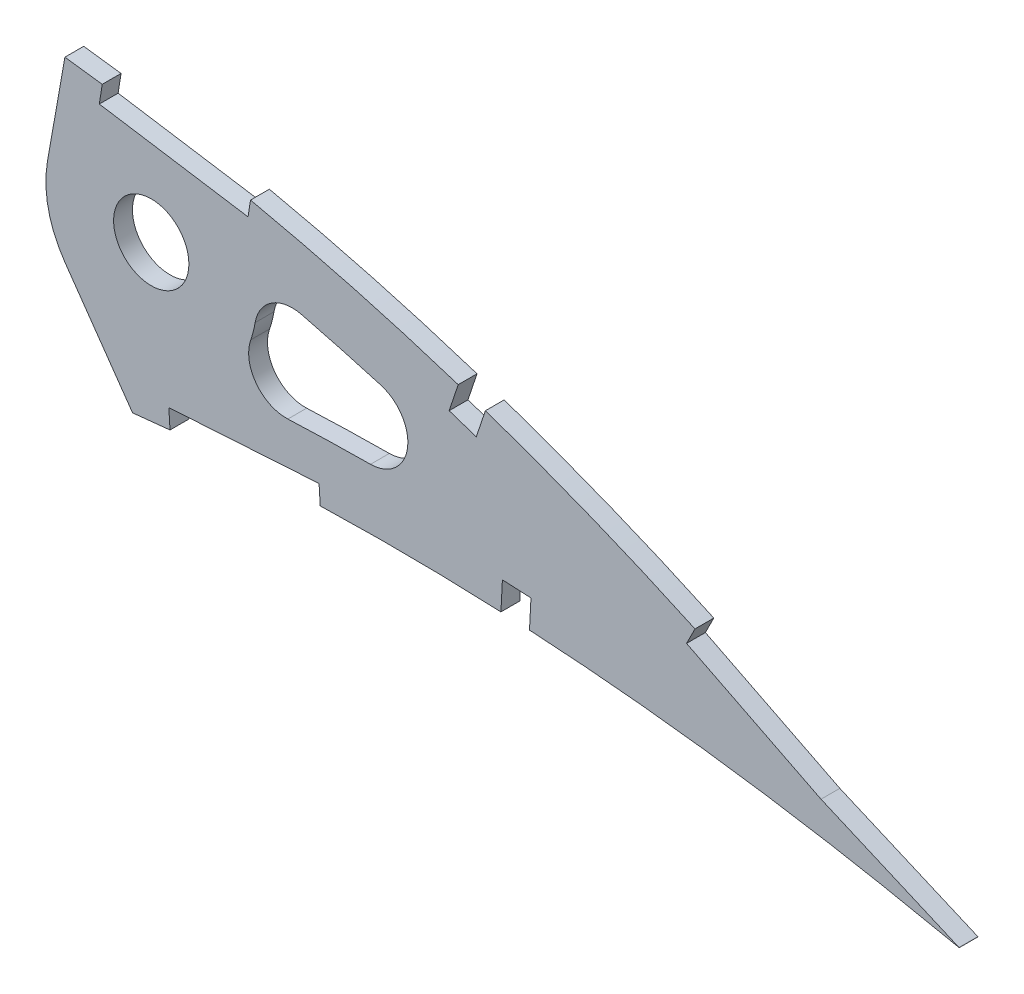
SolidWorks part; units mm, degrees
material "Pine"
ref_plane "Front Plane" through (0, 0, 0) normal (0, 0, 1) x (1, 0, 0)
ref_plane "Top Plane" through (0, 0, 0) normal (0, 1, 0) x (1, 0, 0)
ref_plane "Right Plane" through (0, 0, 0) normal (1, 0, 0) x (0, 0, -1)
curve "Curve1"
  spline degree 3 poles (0, 0, 0) (0.1249, -0.5894, 0) (0.3751, -1.7709, 0) (1.0551, -3.4717, 0) (1.9543, -5.1067, 0) (3.0917, -6.6716, 0) (4.4597, -8.1658, 0) (6.0551, -9.5909, 0) (7.8766, -10.9463, 0) (9.9217, -12.2312, 0) (12.1874, -13.447, 0) (14.6712, -14.593, 0) (17.3708, -15.6688, 0) (20.2833, -16.6729, 0) (23.4051, -17.607, 0) (26.7332, -18.4687, 0) (30.2639, -19.2592, 0) (33.9938, -19.9766, 0) (37.9188, -20.6214, 0) (42.0348, -21.1935, 0) (46.3376, -21.6931, 0) (50.823, -22.1192, 0) (55.4866, -22.4726, 0) (60.3236, -22.7538, 0) (65.3294, -22.9634, 0) (70.4993, -23.1008, 0) (75.828, -23.1681, 0) (81.3109, -23.1662, 0) (86.9426, -23.0948, 0) (92.7182, -22.9577, 0) (98.6323, -22.754, 0) (104.6794, -22.4863, 0) (110.8541, -22.1572, 0) (117.1509, -21.7679, 0) (123.5642, -21.32, 0) (130.0885, -20.8172, 0) (136.7178, -20.2607, 0) (143.4464, -19.6538, 0) (150.2683, -18.9994, 0) (157.1776, -18.2998, 0) (164.1682, -17.5581, 0) (171.2339, -16.7767, 0) (178.3687, -15.9599, 0) (185.566, -15.1091, 0) (192.8198, -14.2292, 0) (200.1233, -13.3218, 0) (207.4703, -12.3905, 0) (214.8542, -11.4396, 0) (222.2681, -10.469, 0) (229.7058, -9.4856, 0) (237.1601, -8.4887, 0) (244.6246, -7.4833, 0) (252.0922, -6.4726, 0) (259.5558, -5.4569, 0) (267.0088, -4.4404, 0) (274.4442, -3.4259, 0) (281.8548, -2.4135, 0) (289.2339, -1.4081, 0) (296.574, -0.4098, 0) (303.8684, 0.5795, 0) (311.1101, 1.5569, 0) (318.2922, 2.521, 0) (325.4074, 3.4714, 0) (332.4485, 4.4082, 0) (339.3029, 5.3032, 0) (345.9529, 6.204, 0) (352.4207, 6.9424, 0) (358.808, 7.5727, 0) (365.1214, 8.0894, 0) (371.3533, 8.5001, 0) (377.4966, 8.8075, 0) (383.544, 9.0161, 0) (389.4878, 9.132, 0) (395.3205, 9.1582, 0) (401.0343, 9.1029, 0) (406.6218, 8.9708, 0) (412.075, 8.7675, 0) (417.3864, 8.5002, 0) (422.5485, 8.1759, 0) (427.5535, 7.7996, 0) (432.3944, 7.38, 0) (437.0637, 6.9232, 0) (441.5544, 6.4344, 0) (445.8598, 5.924, 0) (449.973, 5.3952, 0) (453.8879, 4.8568, 0) (457.5982, 4.3142, 0) (461.0979, 3.7743, 0) (464.3817, 3.2423, 0) (467.4441, 2.7253, 0) (470.2803, 2.228, 0) (472.8856, 1.7553, 0) (475.2562, 1.3133, 0) (477.3874, 0.904, 0) (479.2765, 0.5343, 0) (480.9199, 0.2058, 0) (482.3151, -0.077, 0) (483.4599, -0.3128, 0) (484.3523, -0.4979, 0) (484.9907, -0.6325, 0) (485.3743, -0.7125, 0) (485.5448, -0.7489, 0) (485.5874, -0.758, 0) knots 0 0 0 0 0.003638 0.007293 0.011028 0.014901 0.018963 0.023258 0.027821 0.032679 0.037853 0.043362 0.049215 0.055422 0.061989 0.068918 0.076211 0.083868 0.091887 0.100266 0.109 0.118085 0.127515 0.137285 0.147388 0.157816 0.168563 0.179619 0.190977 0.202627 0.21456 0.226767 0.239236 0.251959 0.264924 0.27812 0.291536 0.30516 0.318981 0.332985 0.347163 0.361499 0.375981 0.390597 0.405333 0.420175 0.43511 0.450124 0.465203 0.480333 0.495501 0.51069 0.525887 0.541078 0.556247 0.571382 0.586466 0.601485 0.616424 0.631269 0.646007 0.660621 0.675098 0.689423 0.703582 0.716908 0.730009 0.742952 0.755726 0.76832 0.780724 0.792927 0.804916 0.816679 0.828204 0.839475 0.850481 0.861208 0.871639 0.881763 0.891564 0.901027 0.910139 0.918884 0.927249 0.935221 0.942785 0.949928 0.956638 0.962904 0.968712 0.974054 0.978918 0.983297 0.98718 0.990561 0.993433 0.995791 0.99763 0.998946 0.999737 1 1 1 1
curve "Curve2"
  spline degree 3 poles (486.1938, 0.758, 0) (486.1565, 0.781, 0) (486.0077, 0.8729, 0) (485.6723, 1.0786, 0) (485.1139, 1.4213, 0) (484.3321, 1.8984, 0) (483.3276, 2.5088, 0) (482.0999, 3.2482, 0) (480.6498, 4.1141, 0) (478.9775, 5.1026, 0) (477.0833, 6.2089, 0) (474.9678, 7.4286, 0) (472.6313, 8.7548, 0) (470.0748, 10.182, 0) (467.2989, 11.7035, 0) (464.3043, 13.3123, 0) (461.0921, 15.0004, 0) (457.6635, 16.7605, 0) (454.019, 18.5827, 0) (450.1605, 20.4596, 0) (446.0892, 22.3819, 0) (441.8065, 24.3391, 0) (437.3149, 26.3234, 0) (432.6155, 28.3224, 0) (427.7112, 30.3274, 0) (422.6039, 32.3272, 0) (417.2967, 34.3124, 0) (411.7916, 36.2703, 0) (406.0928, 38.1924, 0) (400.203, 40.0661, 0) (394.1264, 41.8812, 0) (387.8666, 43.626, 0) (381.4288, 45.2916, 0) (374.8171, 46.8658, 0) (368.037, 48.3381, 0) (361.0939, 49.6996, 0) (353.9938, 50.9366, 0) (346.7562, 52.0484, 0) (339.4976, 52.9732, 0) (332.2539, 53.8802, 0) (325.021, 54.7322, 0) (317.6998, 55.5482, 0) (310.2971, 56.3235, 0) (302.8205, 57.0556, 0) (295.2774, 57.7415, 0) (287.6757, 58.3791, 0) (280.0227, 58.9648, 0) (272.3266, 59.4977, 0) (264.5949, 59.9731, 0) (256.8359, 60.3907, 0) (249.0573, 60.7475, 0) (241.2675, 61.0411, 0) (233.4745, 61.2698, 0) (225.6865, 61.4312, 0) (217.912, 61.5245, 0) (210.159, 61.547, 0) (202.4359, 61.4984, 0) (194.7508, 61.377, 0) (187.1122, 61.1811, 0) (179.5282, 60.9103, 0) (172.0069, 60.5649, 0) (164.5567, 60.1418, 0) (157.1855, 59.6438, 0) (149.9016, 59.0688, 0) (142.713, 58.4167, 0) (135.6273, 57.6901, 0) (128.6522, 56.887, 0) (121.7954, 56.0099, 0) (115.0642, 55.0603, 0) (108.4663, 54.0378, 0) (102.0087, 52.9453, 0) (95.6983, 51.784, 0) (89.542, 50.5572, 0) (83.5463, 49.2652, 0) (77.7176, 47.912, 0) (72.062, 46.4999, 0) (66.5855, 45.0315, 0) (61.2937, 43.5103, 0) (56.192, 41.9397, 0) (51.2862, 40.3215, 0) (46.5802, 38.6618, 0) (42.0796, 36.9619, 0) (37.788, 35.2268, 0) (33.7103, 33.4591, 0) (29.8497, 31.6641, 0) (26.2104, 29.8437, 0) (22.7951, 28.0033, 0) (19.6072, 26.1454, 0) (16.6497, 24.2737, 0) (13.924, 22.3929, 0) (11.4337, 20.504, 0) (9.1798, 18.612, 0) (7.1636, 16.7197, 0) (5.388, 14.8284, 0) (3.8531, 12.9414, 0) (2.5606, 11.0602, 0) (1.511, 9.1866, 0) (0.7066, 7.3219, 0) (0.1466, 5.4673, 0) (-0.16, 3.6254, 0) (-0.2363, 1.7948, 0) (-0.0786, 0.5974, 0) (0, 0, 0) knots 0 0 0 0 0.000254 0.001015 0.002283 0.004057 0.006331 0.009105 0.012374 0.016134 0.02038 0.025106 0.030306 0.035972 0.0421 0.048678 0.055702 0.06316 0.071046 0.07935 0.088063 0.097176 0.106678 0.116562 0.126814 0.137428 0.148394 0.1597 0.171338 0.183298 0.19557 0.208144 0.221012 0.234162 0.247587 0.261277 0.275223 0.289414 0.303771 0.317689 0.331784 0.34604 0.360444 0.374983 0.38964 0.404403 0.419257 0.434187 0.449177 0.464215 0.479284 0.49437 0.509458 0.524532 0.539579 0.554583 0.56953 0.584403 0.599191 0.613877 0.628447 0.642889 0.657186 0.671326 0.685294 0.699078 0.712665 0.726043 0.739198 0.752118 0.764792 0.777208 0.789356 0.801224 0.812804 0.824083 0.835055 0.84571 0.856038 0.866034 0.875689 0.884998 0.893953 0.902553 0.910789 0.918661 0.926166 0.933303 0.940071 0.946475 0.952518 0.958205 0.963547 0.968557 0.97325 0.977651 0.981787 0.985694 0.989415 0.993001 0.996508 1 1 1 1
sketch "Sketch1" plane through (0, 0, 0) normal (0, 0, 1) x (1, 0, 0)
  line L10 (485.5874, -0.758) -> (490.1477, -1.6846)
  line L24 (486.1938, 0.758) -> (490.1477, -1.6846)
  spline S2 degree 3 poles (-3866.8103, -1018.8258) (79.7559, 75.3438) (-9.1933, 22.1629) (1.0551, -3.4717) (1.9543, -5.1067) (3.0917, -6.6716) (4.4597, -8.1658) (6.0551, -9.5909) (7.8766, -10.9463) (9.9217, -12.2312) (12.1874, -13.447) (14.6712, -14.593) (17.3708, -15.6688) (20.2833, -16.6729) (23.4051, -17.607) (26.7332, -18.4687) (30.2639, -19.2592) (33.9938, -19.9766) (37.9188, -20.6214) (42.0348, -21.1935) (46.3376, -21.6931) (50.823, -22.1192) (55.4866, -22.4726) (60.3236, -22.7538) (65.3294, -22.9634) (70.4993, -23.1008) (75.828, -23.1681) (81.3109, -23.1662) (86.9426, -23.0948) (92.7182, -22.9577) (98.6323, -22.754) (104.6794, -22.4863) (110.8541, -22.1572) (117.1509, -21.7679) (123.5642, -21.32) (130.0885, -20.8172) (136.7178, -20.2607) (143.4464, -19.6538) (150.2683, -18.9994) (157.1776, -18.2998) (164.1682, -17.5581) (171.2339, -16.7767) (178.3687, -15.9599) (185.566, -15.1091) (192.8198, -14.2292) (200.1233, -13.3218) (207.4703, -12.3905) (214.8542, -11.4396) (222.2681, -10.469) (229.7058, -9.4856) (237.1601, -8.4887) (244.6246, -7.4833) (252.0922, -6.4726) (259.5558, -5.4569) (267.0088, -4.4404) (274.4442, -3.4259) (281.8548, -2.4135) (289.2339, -1.4081) (296.574, -0.4098) (303.8684, 0.5795) (311.1101, 1.5569) (318.2922, 2.521) (325.4074, 3.4714) (332.4485, 4.4082) (339.3029, 5.3032) (345.9529, 6.204) (352.4207, 6.9424) (358.808, 7.5727) (365.1214, 8.0894) (371.3533, 8.5001) (377.4966, 8.8075) (383.544, 9.0161) (389.4878, 9.132) (395.3205, 9.1582) (401.0343, 9.1029) (406.6218, 8.9708) (412.075, 8.7675) (417.3864, 8.5002) (422.5485, 8.1759) (427.5535, 7.7996) (432.3944, 7.38) (437.0637, 6.9232) (441.5544, 6.4344) (445.8598, 5.924) (449.973, 5.3952) (453.8879, 4.8568) (457.5982, 4.3142) (461.0979, 3.7743) (464.3817, 3.2423) (467.4441, 2.7253) (470.2803, 2.228) (472.8856, 1.7553) (475.2562, 1.3133) (477.3874, 0.904) (479.2765, 0.5343) (480.9199, 0.2058) (482.3151, -0.077) (483.4599, -0.3128) (484.3523, -0.4979) (484.9907, -0.6325) (504.0158, -4.6034) (520.901, -17.6411) (1368.8084, 3899.3631) knots -0.155184 -0.155184 -0.155184 -0.155184 0.003638 0.007293 0.011028 0.014901 0.018963 0.023258 0.027821 0.032679 0.037853 0.043362 0.049215 0.055422 0.061989 0.068918 0.076211 0.083868 0.091887 0.100266 0.109 0.118085 0.127515 0.137285 0.147388 0.157816 0.168563 0.179619 0.190977 0.202627 0.21456 0.226767 0.239236 0.251959 0.264924 0.27812 0.291536 0.30516 0.318981 0.332985 0.347163 0.361499 0.375981 0.390597 0.405333 0.420175 0.43511 0.450124 0.465203 0.480333 0.495501 0.51069 0.525887 0.541078 0.556247 0.571382 0.586466 0.601485 0.616424 0.631269 0.646007 0.660621 0.675098 0.689423 0.703582 0.716908 0.730009 0.742952 0.755726 0.76832 0.780724 0.792927 0.804916 0.816679 0.828204 0.839475 0.850481 0.861208 0.871639 0.881763 0.891564 0.901027 0.910139 0.918884 0.927249 0.935221 0.942785 0.949928 0.956638 0.962904 0.968712 0.974054 0.978918 0.983297 0.98718 0.990561 0.993433 0.995791 0.99763 0.998946 0.999737 1.115177 1.115177 1.115177 1.115177 only from (0, 0) to (485.5874, -0.758) construction
  spline S3 degree 3 poles (2637.6242, 3371.1949) (518.0891, -28.6046) (504.1645, -10.2642) (485.6723, 1.0786) (485.1139, 1.4213) (484.3321, 1.8984) (483.3276, 2.5088) (482.0999, 3.2482) (480.6498, 4.1141) (478.9775, 5.1026) (477.0833, 6.2089) (474.9678, 7.4286) (472.6313, 8.7548) (470.0748, 10.182) (467.2989, 11.7035) (464.3043, 13.3123) (461.0921, 15.0004) (457.6635, 16.7605) (454.019, 18.5827) (450.1605, 20.4596) (446.0892, 22.3819) (441.8065, 24.3391) (437.3149, 26.3234) (432.6155, 28.3224) (427.7112, 30.3274) (422.6039, 32.3272) (417.2967, 34.3124) (411.7916, 36.2703) (406.0928, 38.1924) (400.203, 40.0661) (394.1264, 41.8812) (387.8666, 43.626) (381.4288, 45.2916) (374.8171, 46.8658) (368.037, 48.3381) (361.0939, 49.6996) (353.9938, 50.9366) (346.7562, 52.0484) (339.4976, 52.9732) (332.2539, 53.8802) (325.021, 54.7322) (317.6998, 55.5482) (310.2971, 56.3235) (302.8205, 57.0556) (295.2774, 57.7415) (287.6757, 58.3791) (280.0227, 58.9648) (272.3266, 59.4977) (264.5949, 59.9731) (256.8359, 60.3907) (249.0573, 60.7475) (241.2675, 61.0411) (233.4745, 61.2698) (225.6865, 61.4312) (217.912, 61.5245) (210.159, 61.547) (202.4359, 61.4984) (194.7508, 61.377) (187.1122, 61.1811) (179.5282, 60.9103) (172.0069, 60.5649) (164.5567, 60.1418) (157.1855, 59.6438) (149.9016, 59.0688) (142.713, 58.4167) (135.6273, 57.6901) (128.6522, 56.887) (121.7954, 56.0099) (115.0642, 55.0603) (108.4663, 54.0378) (102.0087, 52.9453) (95.6983, 51.784) (89.542, 50.5572) (83.5463, 49.2652) (77.7176, 47.912) (72.062, 46.4999) (66.5855, 45.0315) (61.2937, 43.5103) (56.192, 41.9397) (51.2862, 40.3215) (46.5802, 38.6618) (42.0796, 36.9619) (37.788, 35.2268) (33.7103, 33.4591) (29.8497, 31.6641) (26.2104, 29.8437) (22.7951, 28.0033) (19.6072, 26.1454) (16.6497, 24.2737) (13.924, 22.3929) (11.4337, 20.504) (9.1798, 18.612) (7.1636, 16.7197) (5.388, 14.8284) (3.8531, 12.9414) (2.5606, 11.0602) (1.511, 9.1866) (0.7066, 7.3219) (0.1466, 5.4673) (-0.16, 3.6254) (-1.3078, -23.9112) (100.477, -44.4073) (-3985.5392, -325.5751) knots -0.123624 -0.123624 -0.123624 -0.123624 0.000254 0.001015 0.002283 0.004057 0.006331 0.009105 0.012374 0.016134 0.02038 0.025106 0.030306 0.035972 0.0421 0.048678 0.055702 0.06316 0.071046 0.07935 0.088063 0.097176 0.106678 0.116562 0.126814 0.137428 0.148394 0.1597 0.171338 0.183298 0.19557 0.208144 0.221012 0.234162 0.247587 0.261277 0.275223 0.289414 0.303771 0.317689 0.331784 0.34604 0.360444 0.374983 0.38964 0.404403 0.419257 0.434187 0.449177 0.464215 0.479284 0.49437 0.509458 0.524532 0.539579 0.554583 0.56953 0.584403 0.599191 0.613877 0.628447 0.642889 0.657186 0.671326 0.685294 0.699078 0.712665 0.726043 0.739198 0.752118 0.764792 0.777208 0.789356 0.801224 0.812804 0.824083 0.835055 0.84571 0.856038 0.866034 0.875689 0.884998 0.893953 0.902553 0.910789 0.918661 0.926166 0.933303 0.940071 0.946475 0.952518 0.958205 0.963547 0.968557 0.97325 0.977651 0.981787 0.985694 0.989415 0.993001 0.996508 1.148636 1.148636 1.148636 1.148636 only from (486.1938, 0.758) to (0, 0) construction
  spline S4 degree 3 poles (0, 0) (0.1249, -0.5894) (0.3751, -1.7709) (1.0551, -3.4717) (1.9543, -5.1067) (3.0917, -6.6716) (4.4597, -8.1658) (6.0551, -9.5909) (7.8766, -10.9463) (9.9217, -12.2312) (12.1874, -13.447) (14.6712, -14.593) (17.3708, -15.6688) (20.2833, -16.6729) (23.4051, -17.607) (26.7332, -18.4687) (30.2639, -19.2592) (33.9938, -19.9766) (37.9188, -20.6214) (42.0348, -21.1935) (46.3376, -21.6931) (50.823, -22.1192) (55.4866, -22.4726) (60.3236, -22.7538) (65.3294, -22.9634) (70.4993, -23.1008) (75.828, -23.1681) (81.3109, -23.1662) (86.9426, -23.0948) (92.7182, -22.9577) (98.6323, -22.754) (104.6794, -22.4863) (110.8541, -22.1572) (117.1509, -21.7679) (123.5642, -21.32) (130.0885, -20.8172) (136.7178, -20.2607) (143.4464, -19.6538) (150.2683, -18.9994) (157.1776, -18.2998) (164.1682, -17.5581) (171.2339, -16.7767) (178.3687, -15.9599) (185.566, -15.1091) (192.8198, -14.2292) (200.1233, -13.3218) (207.4703, -12.3905) (214.8542, -11.4396) (222.2681, -10.469) (229.7058, -9.4856) (237.1601, -8.4887) (244.6246, -7.4833) (252.0922, -6.4726) (259.5558, -5.4569) (267.0088, -4.4404) (274.4442, -3.4259) (281.8548, -2.4135) (289.2339, -1.4081) (296.574, -0.4098) (303.8684, 0.5795) (311.1101, 1.5569) (318.2922, 2.521) (325.4074, 3.4714) (332.4485, 4.4082) (339.3029, 5.3032) (345.9529, 6.204) (352.4207, 6.9424) (358.808, 7.5727) (365.1214, 8.0894) (371.3533, 8.5001) (377.4966, 8.8075) (383.544, 9.0161) (389.4878, 9.132) (395.3205, 9.1582) (401.0343, 9.1029) (406.6218, 8.9708) (412.075, 8.7675) (417.3864, 8.5002) (422.5485, 8.1759) (427.5535, 7.7996) (432.3944, 7.38) (437.0637, 6.9232) (441.5544, 6.4344) (445.8598, 5.924) (449.973, 5.3952) (453.8879, 4.8568) (457.5982, 4.3142) (461.0979, 3.7743) (464.3817, 3.2423) (467.4441, 2.7253) (470.2803, 2.228) (472.8856, 1.7553) (475.2562, 1.3133) (477.3874, 0.904) (479.2765, 0.5343) (480.9199, 0.2058) (482.3151, -0.077) (483.4599, -0.3128) (484.3523, -0.4979) (484.9907, -0.6325) (485.3743, -0.7125) (485.5448, -0.7489) (485.5874, -0.758) knots 0 0 0 0 0.003638 0.007293 0.011028 0.014901 0.018963 0.023258 0.027821 0.032679 0.037853 0.043362 0.049215 0.055422 0.061989 0.068918 0.076211 0.083868 0.091887 0.100266 0.109 0.118085 0.127515 0.137285 0.147388 0.157816 0.168563 0.179619 0.190977 0.202627 0.21456 0.226767 0.239236 0.251959 0.264924 0.27812 0.291536 0.30516 0.318981 0.332985 0.347163 0.361499 0.375981 0.390597 0.405333 0.420175 0.43511 0.450124 0.465203 0.480333 0.495501 0.51069 0.525887 0.541078 0.556247 0.571382 0.586466 0.601485 0.616424 0.631269 0.646007 0.660621 0.675098 0.689423 0.703582 0.716908 0.730009 0.742952 0.755726 0.76832 0.780724 0.792927 0.804916 0.816679 0.828204 0.839475 0.850481 0.861208 0.871639 0.881763 0.891564 0.901027 0.910139 0.918884 0.927249 0.935221 0.942785 0.949928 0.956638 0.962904 0.968712 0.974054 0.978918 0.983297 0.98718 0.990561 0.993433 0.995791 0.99763 0.998946 0.999737 1 1 1 1
  spline S5 degree 3 poles (486.1938, 0.758) (486.1565, 0.781) (486.0077, 0.8729) (485.6723, 1.0786) (485.1139, 1.4213) (484.3321, 1.8984) (483.3276, 2.5088) (482.0999, 3.2482) (480.6498, 4.1141) (478.9775, 5.1026) (477.0833, 6.2089) (474.9678, 7.4286) (472.6313, 8.7548) (470.0748, 10.182) (467.2989, 11.7035) (464.3043, 13.3123) (461.0921, 15.0004) (457.6635, 16.7605) (454.019, 18.5827) (450.1605, 20.4596) (446.0892, 22.3819) (441.8065, 24.3391) (437.3149, 26.3234) (432.6155, 28.3224) (427.7112, 30.3274) (422.6039, 32.3272) (417.2967, 34.3124) (411.7916, 36.2703) (406.0928, 38.1924) (400.203, 40.0661) (394.1264, 41.8812) (387.8666, 43.626) (381.4288, 45.2916) (374.8171, 46.8658) (368.037, 48.3381) (361.0939, 49.6996) (353.9938, 50.9366) (346.7562, 52.0484) (339.4976, 52.9732) (332.2539, 53.8802) (325.021, 54.7322) (317.6998, 55.5482) (310.2971, 56.3235) (302.8205, 57.0556) (295.2774, 57.7415) (287.6757, 58.3791) (280.0227, 58.9648) (272.3266, 59.4977) (264.5949, 59.9731) (256.8359, 60.3907) (249.0573, 60.7475) (241.2675, 61.0411) (233.4745, 61.2698) (225.6865, 61.4312) (217.912, 61.5245) (210.159, 61.547) (202.4359, 61.4984) (194.7508, 61.377) (187.1122, 61.1811) (179.5282, 60.9103) (172.0069, 60.5649) (164.5567, 60.1418) (157.1855, 59.6438) (149.9016, 59.0688) (142.713, 58.4167) (135.6273, 57.6901) (128.6522, 56.887) (121.7954, 56.0099) (115.0642, 55.0603) (108.4663, 54.0378) (102.0087, 52.9453) (95.6983, 51.784) (89.542, 50.5572) (83.5463, 49.2652) (77.7176, 47.912) (72.062, 46.4999) (66.5855, 45.0315) (61.2937, 43.5103) (56.192, 41.9397) (51.2862, 40.3215) (46.5802, 38.6618) (42.0796, 36.9619) (37.788, 35.2268) (33.7103, 33.4591) (29.8497, 31.6641) (26.2104, 29.8437) (22.7951, 28.0033) (19.6072, 26.1454) (16.6497, 24.2737) (13.924, 22.3929) (11.4337, 20.504) (9.1798, 18.612) (7.1636, 16.7197) (5.388, 14.8284) (3.8531, 12.9414) (2.5606, 11.0602) (1.511, 9.1866) (0.7066, 7.3219) (0.1466, 5.4673) (-0.16, 3.6254) (-0.2363, 1.7948) (-0.0786, 0.5974) (0, 0) knots 0 0 0 0 0.000254 0.001015 0.002283 0.004057 0.006331 0.009105 0.012374 0.016134 0.02038 0.025106 0.030306 0.035972 0.0421 0.048678 0.055702 0.06316 0.071046 0.07935 0.088063 0.097176 0.106678 0.116562 0.126814 0.137428 0.148394 0.1597 0.171338 0.183298 0.19557 0.208144 0.221012 0.234162 0.247587 0.261277 0.275223 0.289414 0.303771 0.317689 0.331784 0.34604 0.360444 0.374983 0.38964 0.404403 0.419257 0.434187 0.449177 0.464215 0.479284 0.49437 0.509458 0.524532 0.539579 0.554583 0.56953 0.584403 0.599191 0.613877 0.628447 0.642889 0.657186 0.671326 0.685294 0.699078 0.712665 0.726043 0.739198 0.752118 0.764792 0.777208 0.789356 0.801224 0.812804 0.824083 0.835055 0.84571 0.856038 0.866034 0.875689 0.884998 0.893953 0.902553 0.910789 0.918661 0.926166 0.933303 0.940071 0.946475 0.952518 0.958205 0.963547 0.968557 0.97325 0.977651 0.981787 0.985694 0.989415 0.993001 0.996508 1 1 1 1
extrude "Boss-Extrude1" add sketch "Sketch1" along normal blind 3.175
sketch "Sketch5" plane through (0, 0, 3.175) normal (0, 0, 1) x (1, 0, 0)
  line L0 (336.323, 36.32) -> (339.2642, 53)
  line L1 (339.2684, 23.0344) -> (350.6801, 6.7368)
  line L2 (353.8329, 33.2326) -> (374.466, 33.2326)
  circle A0 centre (353.8329, 33.2326) radius 6.35
  circle A1 centre (353.8329, 33.2326) radius 6.35
  circle A2 centre (353.8329, 33.2326) radius 17.78
  spline S0 degree 3 poles (-1939.0794, -487.5307) (48.5631, 55.4905) (-7.2206, 17.2286) (1.0551, -3.4717) (1.9543, -5.1067) (3.0917, -6.6716) (4.4597, -8.1658) (6.0551, -9.5909) (7.8766, -10.9463) (9.9217, -12.2312) (12.1874, -13.447) (14.6712, -14.593) (17.3708, -15.6688) (20.2833, -16.6729) (23.4051, -17.607) (26.7332, -18.4687) (30.2639, -19.2592) (33.9938, -19.9766) (37.9188, -20.6214) (42.0348, -21.1935) (46.3376, -21.6931) (50.823, -22.1192) (55.4866, -22.4726) (60.3236, -22.7538) (65.3294, -22.9634) (70.4993, -23.1008) (75.828, -23.1681) (81.3109, -23.1662) (86.9426, -23.0948) (92.7182, -22.9577) (98.6323, -22.754) (104.6794, -22.4863) (110.8541, -22.1572) (117.1509, -21.7679) (123.5642, -21.32) (130.0885, -20.8172) (136.7178, -20.2607) (143.4464, -19.6538) (150.2683, -18.9994) (157.1776, -18.2998) (164.1682, -17.5581) (171.2339, -16.7767) (178.3687, -15.9599) (185.566, -15.1091) (192.8198, -14.2292) (200.1233, -13.3218) (207.4703, -12.3905) (214.8542, -11.4396) (222.2681, -10.469) (229.7058, -9.4856) (237.1601, -8.4887) (244.6246, -7.4833) (252.0922, -6.4726) (259.5558, -5.4569) (267.0088, -4.4404) (274.4442, -3.4259) (281.8548, -2.4135) (289.2339, -1.4081) (296.574, -0.4098) (303.8684, 0.5795) (311.1101, 1.5569) (318.2922, 2.521) (325.4074, 3.4714) (332.4485, 4.4082) (339.3029, 5.3032) (345.9529, 6.204) (352.4207, 6.9424) (358.808, 7.5727) (365.1214, 8.0894) (371.3533, 8.5001) (377.4966, 8.8075) (383.544, 9.0161) (389.4878, 9.132) (395.3205, 9.1582) (401.0343, 9.1029) (406.6218, 8.9708) (412.075, 8.7675) (417.3864, 8.5002) (422.5485, 8.1759) (427.5535, 7.7996) (432.3944, 7.38) (437.0637, 6.9232) (441.5544, 6.4344) (445.8598, 5.924) (449.973, 5.3952) (453.8879, 4.8568) (457.5982, 4.3142) (461.0979, 3.7743) (464.3817, 3.2423) (467.4441, 2.7253) (470.2803, 2.228) (472.8856, 1.7553) (475.2562, 1.3133) (477.3874, 0.904) (479.2765, 0.5343) (480.9199, 0.2058) (482.3151, -0.077) (483.4599, -0.3128) (484.3523, -0.4979) (484.9907, -0.6325) (500.1693, -3.8005) (513.9154, -12.6904) (943.5402, 1945.4943) knots -0.123191 -0.123191 -0.123191 -0.123191 0.003638 0.007293 0.011028 0.014901 0.018963 0.023258 0.027821 0.032679 0.037853 0.043362 0.049215 0.055422 0.061989 0.068918 0.076211 0.083868 0.091887 0.100266 0.109 0.118085 0.127515 0.137285 0.147388 0.157816 0.168563 0.179619 0.190977 0.202627 0.21456 0.226767 0.239236 0.251959 0.264924 0.27812 0.291536 0.30516 0.318981 0.332985 0.347163 0.361499 0.375981 0.390597 0.405333 0.420175 0.43511 0.450124 0.465203 0.480333 0.495501 0.51069 0.525887 0.541078 0.556247 0.571382 0.586466 0.601485 0.616424 0.631269 0.646007 0.660621 0.675098 0.689423 0.703582 0.716908 0.730009 0.742952 0.755726 0.76832 0.780724 0.792927 0.804916 0.816679 0.828204 0.839475 0.850481 0.861208 0.871639 0.881763 0.891564 0.901027 0.910139 0.918884 0.927249 0.935221 0.942785 0.949928 0.956638 0.962904 0.968712 0.974054 0.978918 0.983297 0.98718 0.990561 0.993433 0.995791 0.99763 0.998946 0.999737 1.091411 1.091411 1.091411 1.091411 only from (0, 0) to (485.5874, -0.758) construction
  spline S1 degree 3 poles (1577.8242, 1676.0308) (512.2068, -21.3963) (500.4185, -7.9664) (485.6723, 1.0786) (485.1139, 1.4213) (484.3321, 1.8984) (483.3276, 2.5088) (482.0999, 3.2482) (480.6498, 4.1141) (478.9775, 5.1026) (477.0833, 6.2089) (474.9678, 7.4286) (472.6313, 8.7548) (470.0748, 10.182) (467.2989, 11.7035) (464.3043, 13.3123) (461.0921, 15.0004) (457.6635, 16.7605) (454.019, 18.5827) (450.1605, 20.4596) (446.0892, 22.3819) (441.8065, 24.3391) (437.3149, 26.3234) (432.6155, 28.3224) (427.7112, 30.3274) (422.6039, 32.3272) (417.2967, 34.3124) (411.7916, 36.2703) (406.0928, 38.1924) (400.203, 40.0661) (394.1264, 41.8812) (387.8666, 43.626) (381.4288, 45.2916) (374.8171, 46.8658) (368.037, 48.3381) (361.0939, 49.6996) (353.9938, 50.9366) (346.7562, 52.0484) (339.4976, 52.9732) (332.2539, 53.8802) (325.021, 54.7322) (317.6998, 55.5482) (310.2971, 56.3235) (302.8205, 57.0556) (295.2774, 57.7415) (287.6757, 58.3791) (280.0227, 58.9648) (272.3266, 59.4977) (264.5949, 59.9731) (256.8359, 60.3907) (249.0573, 60.7475) (241.2675, 61.0411) (233.4745, 61.2698) (225.6865, 61.4312) (217.912, 61.5245) (210.159, 61.547) (202.4359, 61.4984) (194.7508, 61.377) (187.1122, 61.1811) (179.5282, 60.9103) (172.0069, 60.5649) (164.5567, 60.1418) (157.1855, 59.6438) (149.9016, 59.0688) (142.713, 58.4167) (135.6273, 57.6901) (128.6522, 56.887) (121.7954, 56.0099) (115.0642, 55.0603) (108.4663, 54.0378) (102.0087, 52.9453) (95.6983, 51.784) (89.542, 50.5572) (83.5463, 49.2652) (77.7176, 47.912) (72.062, 46.4999) (66.5855, 45.0315) (61.2937, 43.5103) (56.192, 41.9397) (51.2862, 40.3215) (46.5802, 38.6618) (42.0796, 36.9619) (37.788, 35.2268) (33.7103, 33.4591) (29.8497, 31.6641) (26.2104, 29.8437) (22.7951, 28.0033) (19.6072, 26.1454) (16.6497, 24.2737) (13.924, 22.3929) (11.4337, 20.504) (9.1798, 18.612) (7.1636, 16.7197) (5.388, 14.8284) (3.8531, 12.9414) (2.5606, 11.0602) (1.511, 9.1866) (0.7066, 7.3219) (0.1466, 5.4673) (-0.16, 3.6254) (-1.0869, -18.6116) (64.385, -36.0874) (-1990.8444, -185.2686) knots -0.098119 -0.098119 -0.098119 -0.098119 0.000254 0.001015 0.002283 0.004057 0.006331 0.009105 0.012374 0.016134 0.02038 0.025106 0.030306 0.035972 0.0421 0.048678 0.055702 0.06316 0.071046 0.07935 0.088063 0.097176 0.106678 0.116562 0.126814 0.137428 0.148394 0.1597 0.171338 0.183298 0.19557 0.208144 0.221012 0.234162 0.247587 0.261277 0.275223 0.289414 0.303771 0.317689 0.331784 0.34604 0.360444 0.374983 0.38964 0.404403 0.419257 0.434187 0.449177 0.464215 0.479284 0.49437 0.509458 0.524532 0.539579 0.554583 0.56953 0.584403 0.599191 0.613877 0.628447 0.642889 0.657186 0.671326 0.685294 0.699078 0.712665 0.726043 0.739198 0.752118 0.764792 0.777208 0.789356 0.801224 0.812804 0.824083 0.835055 0.84571 0.856038 0.866034 0.875689 0.884998 0.893953 0.902553 0.910789 0.918661 0.926166 0.933303 0.940071 0.946475 0.952518 0.958205 0.963547 0.968557 0.97325 0.977651 0.981787 0.985694 0.989415 0.993001 0.996508 1.117993 1.117993 1.117993 1.117993 only from (486.1938, 0.758) to (0, 0) construction
  spline S2 degree 3 poles (0, 0) (0.1249, -0.5894) (0.3751, -1.7709) (1.0551, -3.4717) (1.9543, -5.1067) (3.0917, -6.6716) (4.4597, -8.1658) (6.0551, -9.5909) (7.8766, -10.9463) (9.9217, -12.2312) (12.1874, -13.447) (14.6712, -14.593) (17.3708, -15.6688) (20.2833, -16.6729) (23.4051, -17.607) (26.7332, -18.4687) (30.2639, -19.2592) (33.9938, -19.9766) (37.9188, -20.6214) (42.0348, -21.1935) (46.3376, -21.6931) (50.823, -22.1192) (55.4866, -22.4726) (60.3236, -22.7538) (65.3294, -22.9634) (70.4993, -23.1008) (75.828, -23.1681) (81.3109, -23.1662) (86.9426, -23.0948) (92.7182, -22.9577) (98.6323, -22.754) (104.6794, -22.4863) (110.8541, -22.1572) (117.1509, -21.7679) (123.5642, -21.32) (130.0885, -20.8172) (136.7178, -20.2607) (143.4464, -19.6538) (150.2683, -18.9994) (157.1776, -18.2998) (164.1682, -17.5581) (171.2339, -16.7767) (178.3687, -15.9599) (185.566, -15.1091) (192.8198, -14.2292) (200.1233, -13.3218) (207.4703, -12.3905) (214.8542, -11.4396) (222.2681, -10.469) (229.7058, -9.4856) (237.1601, -8.4887) (244.6246, -7.4833) (252.0922, -6.4726) (259.5558, -5.4569) (267.0088, -4.4404) (274.4442, -3.4259) (281.8548, -2.4135) (289.2339, -1.4081) (296.574, -0.4098) (303.8684, 0.5795) (311.1101, 1.5569) (318.2922, 2.521) (325.4074, 3.4714) (332.4485, 4.4082) (339.3029, 5.3032) (345.9529, 6.204) (352.4207, 6.9424) (358.808, 7.5727) (365.1214, 8.0894) (371.3533, 8.5001) (377.4966, 8.8075) (383.544, 9.0161) (389.4878, 9.132) (395.3205, 9.1582) (401.0343, 9.1029) (406.6218, 8.9708) (412.075, 8.7675) (417.3864, 8.5002) (422.5485, 8.1759) (427.5535, 7.7996) (432.3944, 7.38) (437.0637, 6.9232) (441.5544, 6.4344) (445.8598, 5.924) (449.973, 5.3952) (453.8879, 4.8568) (457.5982, 4.3142) (461.0979, 3.7743) (464.3817, 3.2423) (467.4441, 2.7253) (470.2803, 2.228) (472.8856, 1.7553) (475.2562, 1.3133) (477.3874, 0.904) (479.2765, 0.5343) (480.9199, 0.2058) (482.3151, -0.077) (483.4599, -0.3128) (484.3523, -0.4979) (484.9907, -0.6325) (485.3743, -0.7125) (485.5448, -0.7489) (485.5874, -0.758) knots 0 0 0 0 0.003638 0.007293 0.011028 0.014901 0.018963 0.023258 0.027821 0.032679 0.037853 0.043362 0.049215 0.055422 0.061989 0.068918 0.076211 0.083868 0.091887 0.100266 0.109 0.118085 0.127515 0.137285 0.147388 0.157816 0.168563 0.179619 0.190977 0.202627 0.21456 0.226767 0.239236 0.251959 0.264924 0.27812 0.291536 0.30516 0.318981 0.332985 0.347163 0.361499 0.375981 0.390597 0.405333 0.420175 0.43511 0.450124 0.465203 0.480333 0.495501 0.51069 0.525887 0.541078 0.556247 0.571382 0.586466 0.601485 0.616424 0.631269 0.646007 0.660621 0.675098 0.689423 0.703582 0.716908 0.730009 0.742952 0.755726 0.76832 0.780724 0.792927 0.804916 0.816679 0.828204 0.839475 0.850481 0.861208 0.871639 0.881763 0.891564 0.901027 0.910139 0.918884 0.927249 0.935221 0.942785 0.949928 0.956638 0.962904 0.968712 0.974054 0.978918 0.983297 0.98718 0.990561 0.993433 0.995791 0.99763 0.998946 0.999737 1 1 1 1
  spline S3 degree 3 poles (486.1938, 0.758) (486.1565, 0.781) (486.0077, 0.8729) (485.6723, 1.0786) (485.1139, 1.4213) (484.3321, 1.8984) (483.3276, 2.5088) (482.0999, 3.2482) (480.6498, 4.1141) (478.9775, 5.1026) (477.0833, 6.2089) (474.9678, 7.4286) (472.6313, 8.7548) (470.0748, 10.182) (467.2989, 11.7035) (464.3043, 13.3123) (461.0921, 15.0004) (457.6635, 16.7605) (454.019, 18.5827) (450.1605, 20.4596) (446.0892, 22.3819) (441.8065, 24.3391) (437.3149, 26.3234) (432.6155, 28.3224) (427.7112, 30.3274) (422.6039, 32.3272) (417.2967, 34.3124) (411.7916, 36.2703) (406.0928, 38.1924) (400.203, 40.0661) (394.1264, 41.8812) (387.8666, 43.626) (381.4288, 45.2916) (374.8171, 46.8658) (368.037, 48.3381) (361.0939, 49.6996) (353.9938, 50.9366) (346.7562, 52.0484) (339.4976, 52.9732) (332.2539, 53.8802) (325.021, 54.7322) (317.6998, 55.5482) (310.2971, 56.3235) (302.8205, 57.0556) (295.2774, 57.7415) (287.6757, 58.3791) (280.0227, 58.9648) (272.3266, 59.4977) (264.5949, 59.9731) (256.8359, 60.3907) (249.0573, 60.7475) (241.2675, 61.0411) (233.4745, 61.2698) (225.6865, 61.4312) (217.912, 61.5245) (210.159, 61.547) (202.4359, 61.4984) (194.7508, 61.377) (187.1122, 61.1811) (179.5282, 60.9103) (172.0069, 60.5649) (164.5567, 60.1418) (157.1855, 59.6438) (149.9016, 59.0688) (142.713, 58.4167) (135.6273, 57.6901) (128.6522, 56.887) (121.7954, 56.0099) (115.0642, 55.0603) (108.4663, 54.0378) (102.0087, 52.9453) (95.6983, 51.784) (89.542, 50.5572) (83.5463, 49.2652) (77.7176, 47.912) (72.062, 46.4999) (66.5855, 45.0315) (61.2937, 43.5103) (56.192, 41.9397) (51.2862, 40.3215) (46.5802, 38.6618) (42.0796, 36.9619) (37.788, 35.2268) (33.7103, 33.4591) (29.8497, 31.6641) (26.2104, 29.8437) (22.7951, 28.0033) (19.6072, 26.1454) (16.6497, 24.2737) (13.924, 22.3929) (11.4337, 20.504) (9.1798, 18.612) (7.1636, 16.7197) (5.388, 14.8284) (3.8531, 12.9414) (2.5606, 11.0602) (1.511, 9.1866) (0.7066, 7.3219) (0.1466, 5.4673) (-0.16, 3.6254) (-0.2363, 1.7948) (-0.0786, 0.5974) (0, 0) knots 0 0 0 0 0.000254 0.001015 0.002283 0.004057 0.006331 0.009105 0.012374 0.016134 0.02038 0.025106 0.030306 0.035972 0.0421 0.048678 0.055702 0.06316 0.071046 0.07935 0.088063 0.097176 0.106678 0.116562 0.126814 0.137428 0.148394 0.1597 0.171338 0.183298 0.19557 0.208144 0.221012 0.234162 0.247587 0.261277 0.275223 0.289414 0.303771 0.317689 0.331784 0.34604 0.360444 0.374983 0.38964 0.404403 0.419257 0.434187 0.449177 0.464215 0.479284 0.49437 0.509458 0.524532 0.539579 0.554583 0.56953 0.584403 0.599191 0.613877 0.628447 0.642889 0.657186 0.671326 0.685294 0.699078 0.712665 0.726043 0.739198 0.752118 0.764792 0.777208 0.789356 0.801224 0.812804 0.824083 0.835055 0.84571 0.856038 0.866034 0.875689 0.884998 0.893953 0.902553 0.910789 0.918661 0.926166 0.933303 0.940071 0.946475 0.952518 0.958205 0.963547 0.968557 0.97325 0.977651 0.981787 0.985694 0.989415 0.993001 0.996508 1 1 1 1
  spline S4 degree 1 poles (480.8541, -7.8857) (10.0221, 1.7185) knots 0 0 1 1 construction
  spline S5 degree 1 poles (10.0221, 1.7185) (487.707, 9.1785) knots 0 0 1 1 construction
  spline S6 degree 3 poles (480.8541, -7.8857) (480.7201, -7.8029) (480.4589, -7.6425) (479.8783, -7.2863) (478.9124, -6.6962) (476.9448, -5.5034) (473.0052, -3.1584) (465.0526, 1.417) (448.8811, 10.0668) (425.053, 20.9312) (400.3824, 29.6362) (380.244, 35.2169) (367.5068, 38.1191) (357.2621, 40.0741) (349.5101, 41.3746) (341.8335, 42.449) (333.8166, 43.4475) (325.9049, 44.4061) (315.2983, 45.6009) (296.7451, 47.4959) (270.1814, 49.6136) (238.2719, 51.1465) (206.364, 51.5674) (174.5136, 50.7436) (142.8023, 48.4874) (116.597, 45.208) (95.874, 41.5554) (80.5049, 38.2363) (65.3742, 34.2512) (53.0577, 30.2789) (43.4884, 26.6248) (36.4997, 23.6156) (29.7711, 20.3046) (23.4201, 16.6518) (17.6543, 12.6276) (13.6768, 8.9843) (11.4208, 6.112) (10.5313, 4.5112) (10.1421, 3.4379) (10.0302, 2.9559) (9.9731, 2.5067) (9.9642, 2.3114) (9.9656, 2.2504) (9.9657, 2.2359) (9.9791, 2.0811) (9.9996, 1.9002) (10.0148, 1.7763) (10.0221, 1.7185) knots 0 0 0 0 0.000976 0.001951 0.003903 0.007806 0.015611 0.031223 0.062446 0.124891 0.187337 0.21856 0.249783 0.265394 0.281006 0.296617 0.312229 0.32784 0.343451 0.374674 0.43712 0.499566 0.562011 0.624457 0.686903 0.749348 0.780571 0.811794 0.843017 0.87424 0.889851 0.905463 0.921074 0.936686 0.952297 0.967908 0.975714 0.98352 0.987423 0.991326 0.993277 0.995228 0.996204 0.99718 0.998156 0.998643 0.999131 0.999131 0.999131 0.999131
  spline S7 degree 3 poles (10.0221, 1.7185) (10.034, 1.6636) (10.0599, 1.5462) (10.0999, 1.3723) (10.1389, 1.2199) (10.1476, 1.1921) (10.1628, 1.1452) (10.2268, 0.9816) (10.4203, 0.5862) (10.6781, 0.1667) (11.3398, -0.673) (12.618, -1.867) (15.4809, -3.8036) (20.1586, -5.9835) (26.5914, -8.0226) (33.4675, -9.5952) (40.5985, -10.785) (47.8877, -11.6685) (57.7439, -12.5059) (70.2368, -13.025) (85.3646, -13.0282) (100.5676, -12.5574) (120.8957, -11.433) (146.3656, -9.2898) (176.9642, -5.9687) (207.5889, -2.1743) (238.231, 1.8884) (268.9049, 6.0711) (294.4834, 9.566) (312.4086, 11.9846) (322.6494, 13.3534) (329.0537, 14.2071) (334.1907, 14.8818) (338.0026, 15.3833) (341.8382, 15.8997) (345.8011, 16.4075) (349.7595, 16.8632) (355.0135, 17.4179) (364.2536, 18.2584) (377.4648, 19.063) (398.6452, 19.5221) (425.0949, 18.559) (451.3668, 15.6636) (469.5828, 12.7141) (478.6615, 11.0165) (482.841, 10.1846) (484.7931, 9.786) (485.7414, 9.5904) (486.586, 9.4145) (487.1818, 9.2892) (487.5367, 9.2148) (487.707, 9.1785) knots 0.000905 0.000905 0.000905 0.000905 0.001393 0.00188 0.002856 0.003832 0.004808 0.006759 0.00871 0.012613 0.016516 0.024321 0.032127 0.047737 0.063348 0.078959 0.09457 0.110181 0.125792 0.157013 0.188235 0.219457 0.250679 0.313122 0.375565 0.438009 0.500452 0.562896 0.625339 0.656561 0.672172 0.687783 0.695588 0.703394 0.711199 0.719004 0.72681 0.734615 0.750226 0.781448 0.81267 0.875113 0.937557 0.968778 0.984389 0.992195 0.994146 0.996097 0.998049 0.999024 1 1 1 1
  dimension "D1" = 35.56
  dimension "D2" = 10.16
  dimension "D3" = 80
  dimension "D4" = 55
extrude "Cut-Extrude5" cut sketch "Sketch5" against normal through all
sketch "Sketch6" plane through (0, 0, 0) normal (0, 0, -1) x (-1, 0, 0)
  line L0 (-417.6503, 8.4753) -> (-417.6503, 7.6122)
  line L1 (-491.4214, 1.2315) -> (-468.1792, 11.2389)
  line L2 (-417.6503, 7.6122) -> (-412.8307, 7.8598)
  line L3 (-490.1657, -1.6847) -> (-491.4214, 1.2315)
  line L4 (-412.8307, 7.8598) -> (-412.8307, 8.7229)
  line L5 (-468.1792, 11.2389) -> (-445.5766, 22.6173)
  line L6 (-382.3474, 8.9759) -> (-382.3474, 7.8598)
  line L7 (-417.6503, 8.4753) -> (-417.8979, 13.295)
  line L8 (-382.3474, 7.8598) -> (-356.9972, 6.2903)
  line L9 (-417.8979, 13.295) -> (-413.0783, 13.5426)
  line L10 (-356.9972, 6.2903) -> (-356.9972, 7.3864)
  line L11 (-408.6744, 32.2283) -> (-410.2016, 36.8062)
  line L13 (-410.2016, 36.8062) -> (-405.6236, 38.3335)
  line L15 (-382.3474, 8.9759) -> (-382.1488, 12.1446)
  line L17 (-382.1488, 12.1446) -> (-356.7986, 10.5551)
  line L19 (-370.1628, 45.1121) -> (-370.6549, 48.2487)
  line L21 (-370.6549, 48.2487) -> (-345.562, 52.1861)
  line L23 (-466.8364, 8.3603) -> (-490.1657, -1.6847)
  line L25 (-444.149, 19.7814) -> (-466.8364, 8.3603)
  line L27 (-445.5766, 22.6173) -> (-444.149, 19.7814)
  line L31 (-413.0783, 13.5426) -> (-412.8307, 8.7229)
  line L35 (-356.7986, 10.5551) -> (-356.9972, 7.3864)
  line L37 (-404.0964, 33.7555) -> (-408.6744, 32.2283)
  line L39 (-405.6236, 38.3335) -> (-404.0964, 33.7555)
  line L41 (-345.0698, 49.0495) -> (-370.1628, 45.1121)
  line L43 (-345.562, 52.1861) -> (-345.0698, 49.0495)
extrude "Cut-Extrude6" cut sketch "Sketch6" against normal blind 7.62
fillet "Fillet1" radius 6.35 3 edges at (431.7922, 17.6271, 1.5875) (363.1942, 18.1165, 1.5875) (371.1522, 37.2537, 1.5875)
